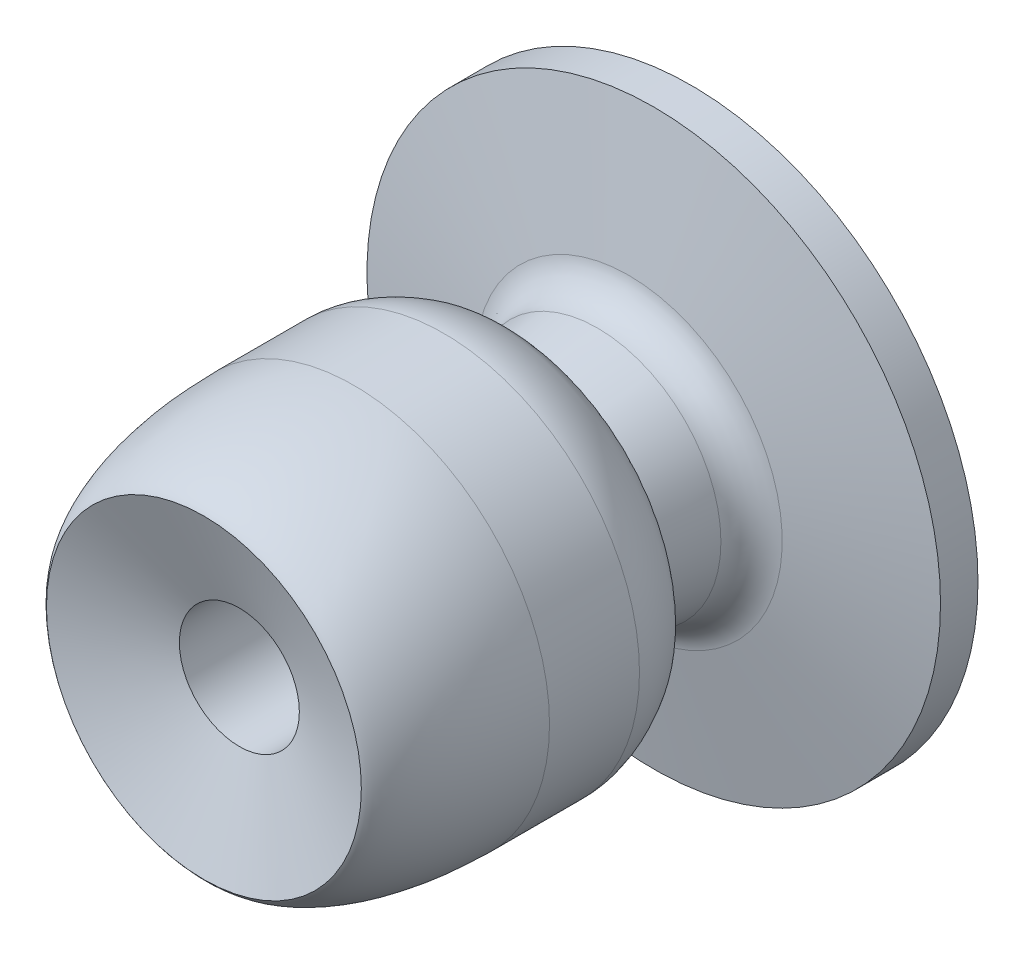
SolidWorks part; units mm, degrees
ref_plane "正面" through (0, 0, 0) normal (0, 0, 1) x (1, 0, 0)
ref_plane "平面" through (0, 0, 0) normal (0, 1, 0) x (1, 0, 0)
ref_plane "右側面" through (0, 0, 0) normal (1, 0, 0) x (0, 0, -1)
sketch "ｽｹｯﾁ1" plane through (0, 0, 0) normal (0, 0, 1) x (1, 0, 0)
  circle A0 centre (0, 0) radius 38.25
  dimension "D1" = 76.5
extrude "ﾎﾞｽ - 押し出し1" add sketch "ｽｹｯﾁ1" along normal blind 5
sketch "ｽｹｯﾁ2" plane through (0, 0, 0) normal (1, 0, 0) x (0, 0, -1)
  line L0 (0, 0) -> (-100, 0) construction
  line L1 (-22, 0) -> (-22, 15)
  line L2 (-22, 15) -> (-9, 17)
  line L3 (-9, 17) -> (-5, 38.25)
  line L4 (0, 38.25) -> (-5, 38.25) construction
  line L5 (-5, 38.25) -> (-5, -38.25) construction
  line L6 (-5, 38.25) -> (-5, 0)
  line L7 (-5, 0) -> (-22, 0)
  line L8 (0, -38.25) -> (0, 38.25) construction
  dimension "D1" = 15
  dimension "D2" = 9
  dimension "D3" = 17
  dimension "D4" = 22
revolve "回転1" add sketch "ｽｹｯﾁ2" angle 360 about L0
fillet "ﾌｨﾚｯﾄ1" radius 5 1 edges at (0, 17, 9)
sketch "ｽｹｯﾁ3" plane through (0, 0, 0) normal (1, 0, 0) x (0, 0, -1)
  line L0 (0, 0) -> (-96.1945, 0) construction
  line L1 (-65, 0) -> (-65, 21) construction
  line L2 (-45, 26.1) -> (-33, 26.1)
  line L3 (-22, 15) -> (-22, 0)
  line L4 (0, -38.25) -> (0, 38.25) construction
  line L5 (-22, 0) -> (-57.3566, 0)
  line L6 (-65, 21) -> (-57.3566, 0)
  spline S0 degree 3 poles (-45, 26.1) (-57.8462, 26.004) (-64.2303, 22.2941) (-65, 21) knots 0 0 0 0 1 1 1 1
  spline S1 degree 3 poles (-33, 26.1) (-30.0101, 26.1) (-26.8208, 24.2541) (-25.6225, 23.558) (-22.4707, 20.9502) (-22, 15) knots 0 0 0 0 0.463324 0.563324 1 1 1 1
  dimension "D1" = 21
  dimension "D2" = 20
  dimension "D3" = 33
  dimension "D4" = 45
  dimension "D5" = 65
revolve "回転2" add sketch "ｽｹｯﾁ3" angle 360 about L0
sketch "ｽｹｯﾁ5" plane through (0, 0, 0) normal (0, 0, -1) x (-1, 0, 0)
  circle A0 centre (0, 0) radius 8
extrude "ｶｯﾄ - 押し出し1" cut sketch "ｽｹｯﾁ5" against normal through all
sketch "ｽｹｯﾁ6" plane through (0, 0, 0) normal (0, 0, -1) x (-1, 0, 0)
  line L1 (10, -10) -> (-10, -10)
  line L2 (10, -10) -> (10, 10)
  line L3 (10, 10) -> (-10, 10)
  line L4 (-10, -10) -> (-10, 10)
  line L5 (10, -10) -> (-10, 10) construction
  line L6 (10, 10) -> (-10, -10) construction
  point P0 (0, 0)
  dimension "D1" = 20
  dimension "D2" = 20
extrude "ﾎﾞｽ - 押し出し2" add sketch "ｽｹｯﾁ6" along normal blind 10
